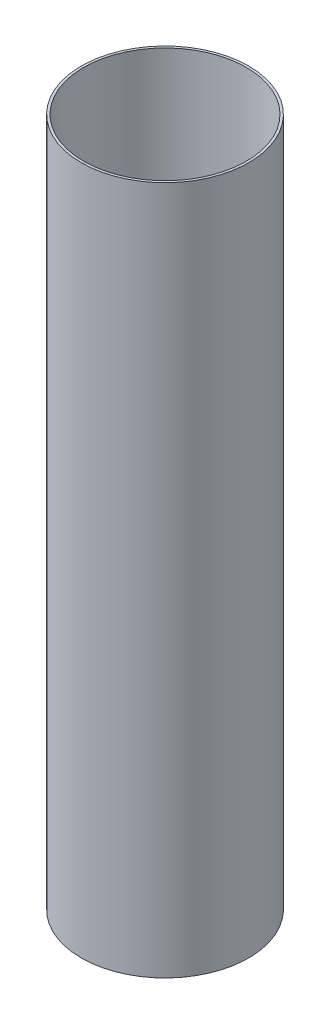
SolidWorks part; units mm, degrees
material "E-Glass Fiber"
ref_plane "Front Plane" through (0, 0, 0) normal (0, 0, 1) x (1, 0, 0)
ref_plane "Top Plane" through (0, 0, 0) normal (0, 1, 0) x (1, 0, 0)
ref_plane "Right Plane" through (0, 0, 0) normal (1, 0, 0) x (0, 0, -1)
sketch "Motor Mount Profile Sketch" plane through (0, 0, 0) normal (0, 1, 0) x (1, 0, 0)
  circle A0 centre (0, 0) radius 50.9778
  circle A1 centre (0, 0) radius 49.53
  dimension "D1" = 101.9556
  dimension "D2" = 99.06
extrude "Motor Mount Body" add sketch "Motor Mount Profile Sketch" along normal blind 419.351
equation "\"Length\"= 16.50988189"
equation "\"Outer Diameter\"= 4.014"
equation "\"Inner Diameter\"= 3.9"
equation "\"Wall Thickness\"= 0.062"
equation "\"D1@Motor Mount Profile Sketch\" = \"Outer Diameter\""
equation "\"D2@Motor Mount Profile Sketch\" = \"Inner Diameter\""
equation "\"D1@Motor Mount Body\" = \"Length\""
